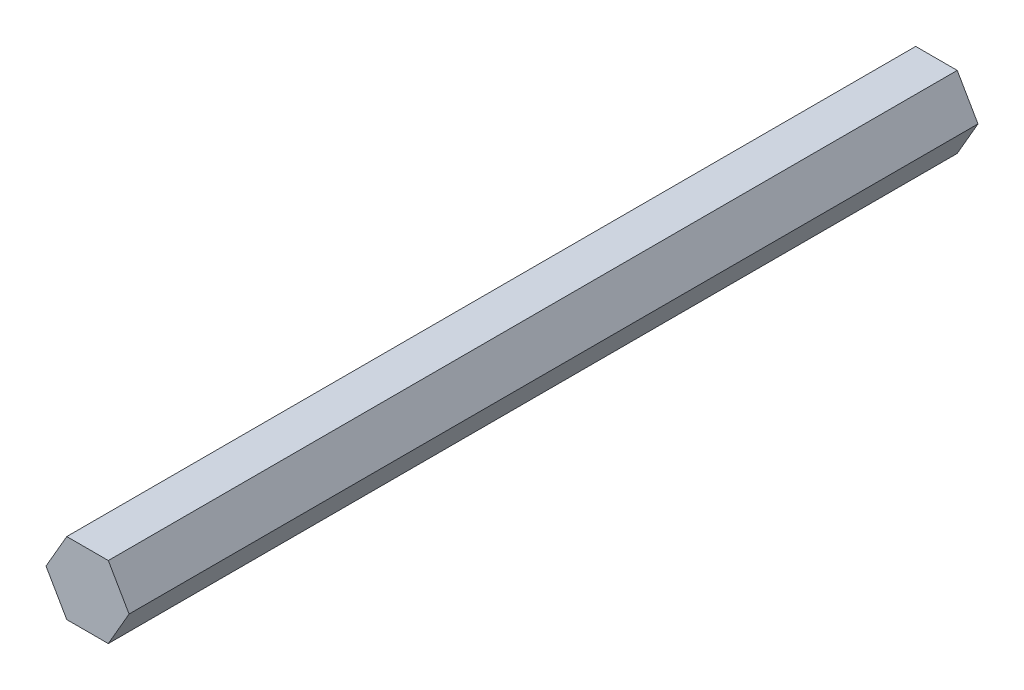
SolidWorks part; units mm, degrees
ref_plane "Front" through (0, 0, 0) normal (0, 0, 1) x (1, 0, 0)
ref_plane "Top" through (0, 0, 0) normal (0, 1, 0) x (1, 0, 0)
ref_plane "Right" through (0, 0, 0) normal (1, 0, 0) x (0, 0, -1)
sketch "Sketch1" plane through (0, 0, 0) normal (0, 0, 1) x (1, 0, 0)
  line L1 (7.3323, 0) -> (3.6662, 6.35)
  line L2 (3.6662, 6.35) -> (-3.6662, 6.35)
  line L3 (-3.6662, 6.35) -> (-7.3323, 0)
  line L4 (-7.3323, 0) -> (-3.6662, -6.35)
  line L5 (-3.6662, -6.35) -> (3.6662, -6.35)
  line L6 (3.6662, -6.35) -> (7.3323, 0)
  circle A0 centre (0, 0) radius 6.35 construction
  dimension "D1" = 12.7
extrude "Boss-Extrude1" add sketch "Sketch1" along normal blind 149.86
sketch "Sketch2" plane through (0, 0, 0) normal (0, 0, -1) x (-1, 0, 0)
  circle A0 centre (0, 0) radius 2.54
  dimension "D1" = 5.08
extrude "Cut-Extrude1" cut sketch "Sketch2" against normal blind 20.574
